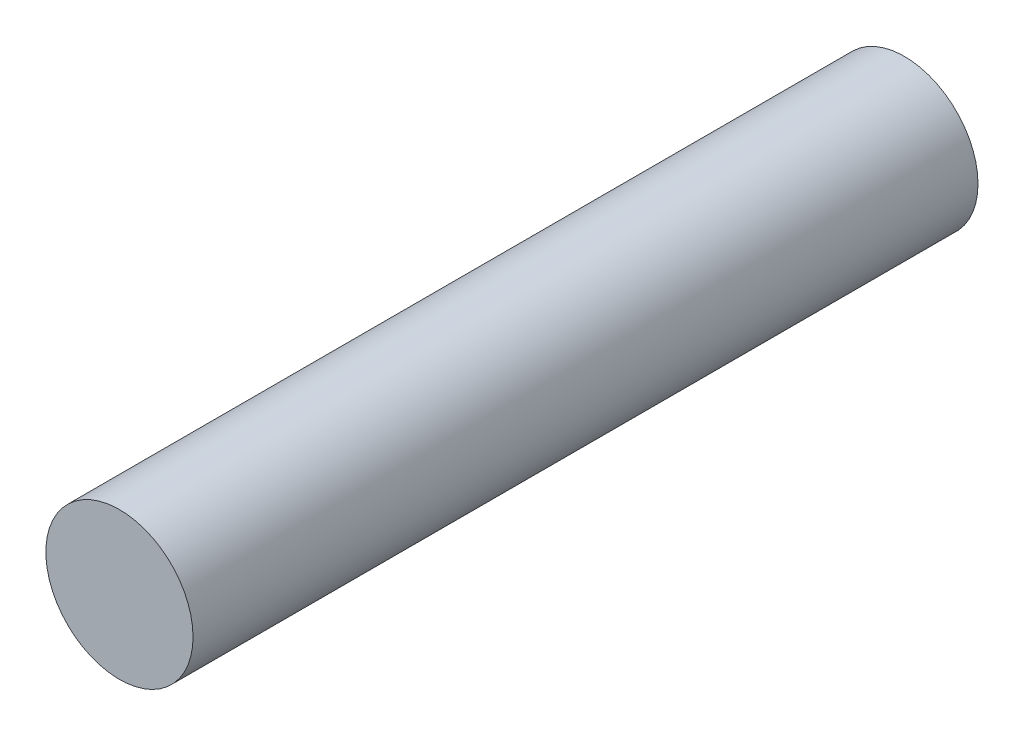
SolidWorks part; units mm, degrees
ref_plane "Front Plane" through (0, 0, 0) normal (0, 0, 1) x (1, 0, 0)
ref_plane "Top Plane" through (0, 0, 0) normal (0, 1, 0) x (1, 0, 0)
ref_plane "Right Plane" through (0, 0, 0) normal (1, 0, 0) x (0, 0, -1)
sketch "Sketch3" plane through (0, 0, 0) normal (0, 0, 1) x (1, 0, 0)
  circle A0 centre (0, 0) radius 4.7625
  dimension "D1" = 9.525
extrude "Boss-Extrude1" add sketch "Sketch3" along normal blind 50.8
